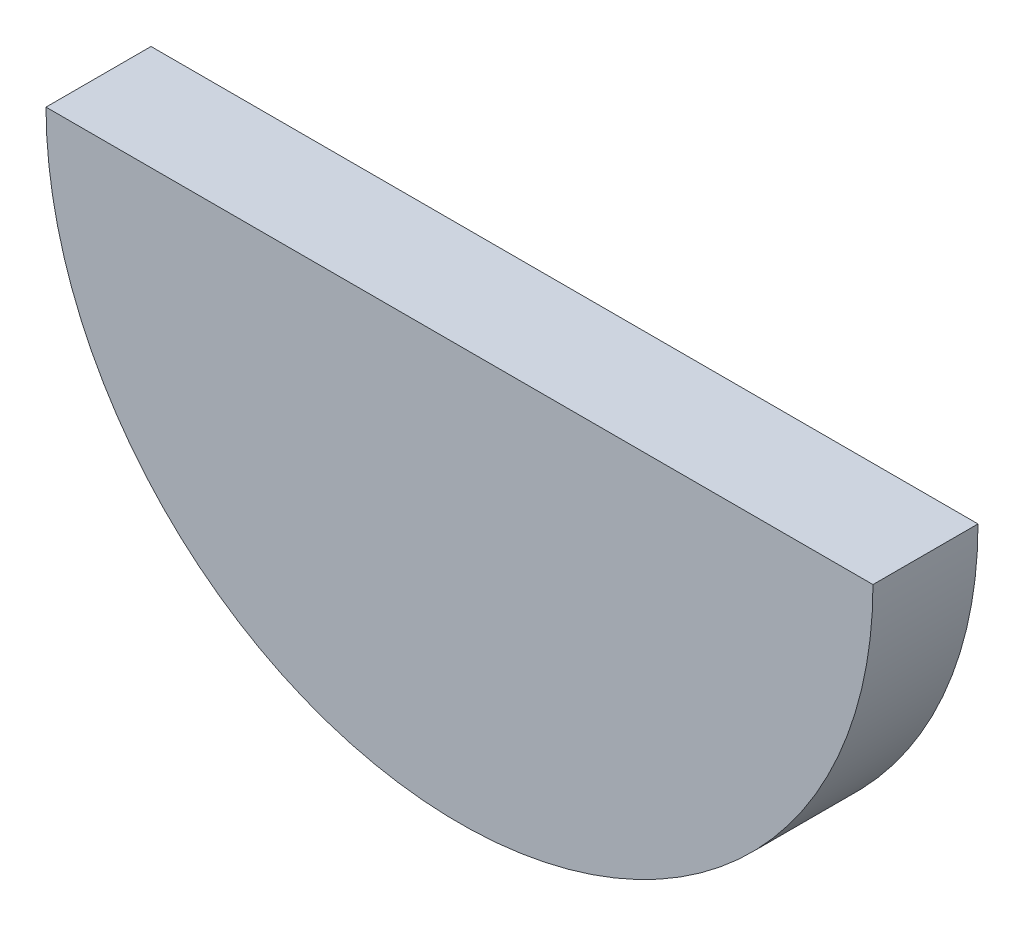
SolidWorks part; units mm, degrees
ref_plane "Front Plane" through (0, 0, 0) normal (0, 0, 1) x (1, 0, 0)
ref_plane "Top Plane" through (0, 0, 0) normal (0, 1, 0) x (1, 0, 0)
ref_plane "Right Plane" through (0, 0, 0) normal (1, 0, 0) x (0, 0, -1)
sketch "Sketch1" plane through (0, 0, 0) normal (0, 0, 1) x (1, 0, 0)
  line L0 (-400, 0) -> (400, 0)
  arc A0 (-400, 0) -> (400, 0) centre (0, 0) ccw
extrude "Boss-Extrude1" add sketch "Sketch1" along normal blind 101.6
